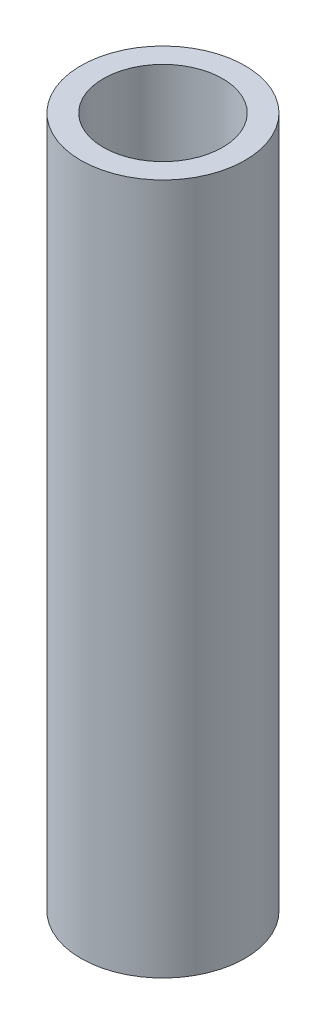
SolidWorks part; units mm, degrees
material "1060 Alloy"
ref_plane "Front Plane" through (0, 0, 0) normal (0, 0, 1) x (1, 0, 0)
ref_plane "Top Plane" through (0, 0, 0) normal (0, 1, 0) x (1, 0, 0)
ref_plane "Right Plane" through (0, 0, 0) normal (1, 0, 0) x (0, 0, -1)
sketch "Sketch1" plane through (0, 0, 0) normal (0, 1, 0) x (1, 0, 0)
  circle A0 centre (0, 0) radius 3.45
  circle A1 centre (0, 0) radius 4.75
  dimension "D1" = 6.9
  dimension "D2" = 9.5
extrude "Boss-Extrude1" add sketch "Sketch1" along normal mid plane 40
